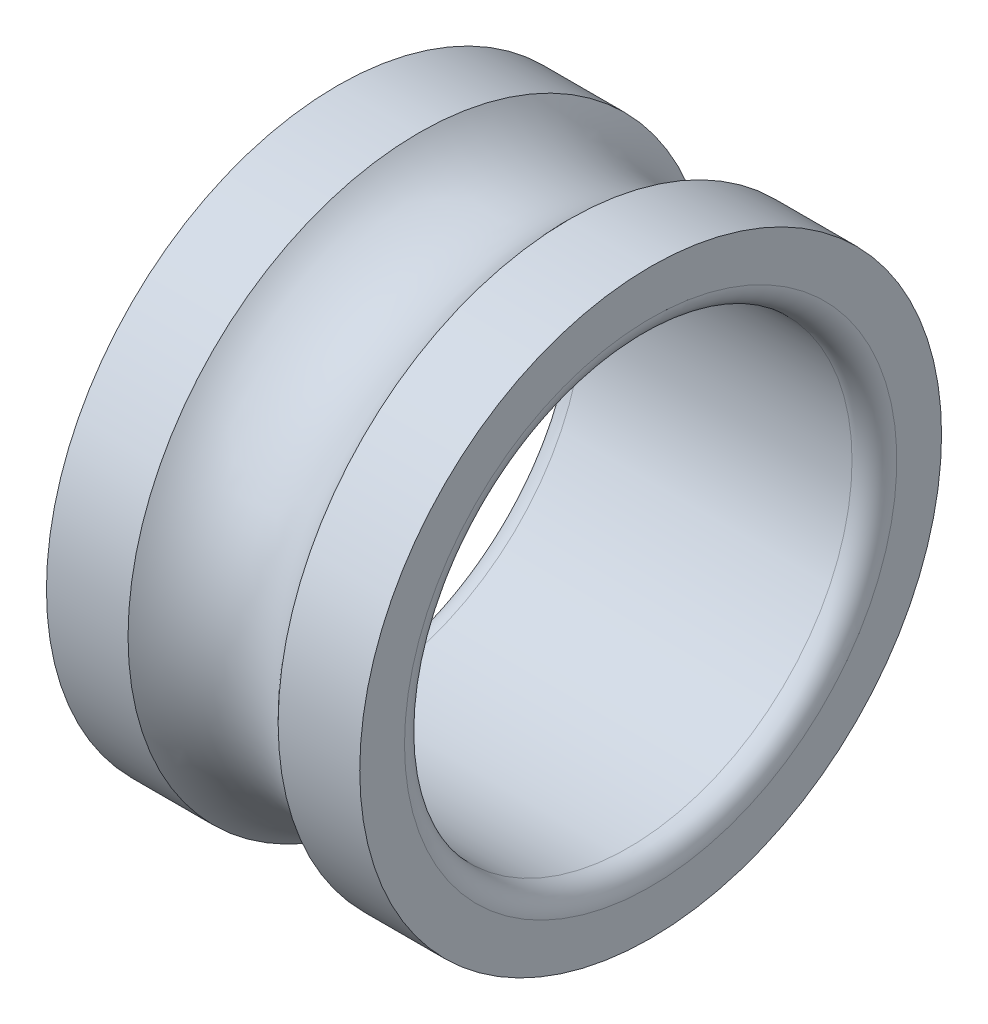
SolidWorks part; units mm, degrees
material "Chrome Stainless Steel"
ref_plane "Front Plane" through (0, 0, 0) normal (0, 0, 1) x (1, 0, 0)
ref_plane "Top Plane" through (0, 0, 0) normal (0, 1, 0) x (1, 0, 0)
ref_plane "Right Plane" through (0, 0, 0) normal (1, 0, 0) x (0, 0, -1)
sketch "Sketch1" plane through (0, 0, 0) normal (0, 0, 1) x (1, 0, 0)
  line L0 (-42.3909, 0) -> (42.6535, 0) construction
  line L1 (0, -30.2792) -> (0, 32.3856) construction
  line L2 (1.6771, 6.5) -> (3.5, 6.5)
  line L3 (-3.5, 5) -> (3.5, 5)
  line L4 (-3.5, 5) -> (-3.5, 6.5)
  line L5 (-3.5, 6.5) -> (-1.6771, 6.5)
  line L6 (3.5, 5) -> (3.5, 6.5)
  line L7 (-3.5, 5) -> (3.5, 6.5) construction
  line L8 (-3.5, 6.5) -> (3.5, 5) construction
  arc A0 (-1.6771, 6.5) -> (1.6771, 6.5) centre (0, 8) ccw
  point P5 (0, 5.75)
  dimension "D5" = 2.25
  dimension "D1" = 1.5
  dimension "D2" = 7
  dimension "D3" = 5
  dimension "D4" = 1.5
revolve "Revolve1" add sketch "Sketch1" angle 360 about L0
fillet "Fillet1" radius 0.5 2 edges at (-3.5, 0, 5) (3.5, 0, 5)
